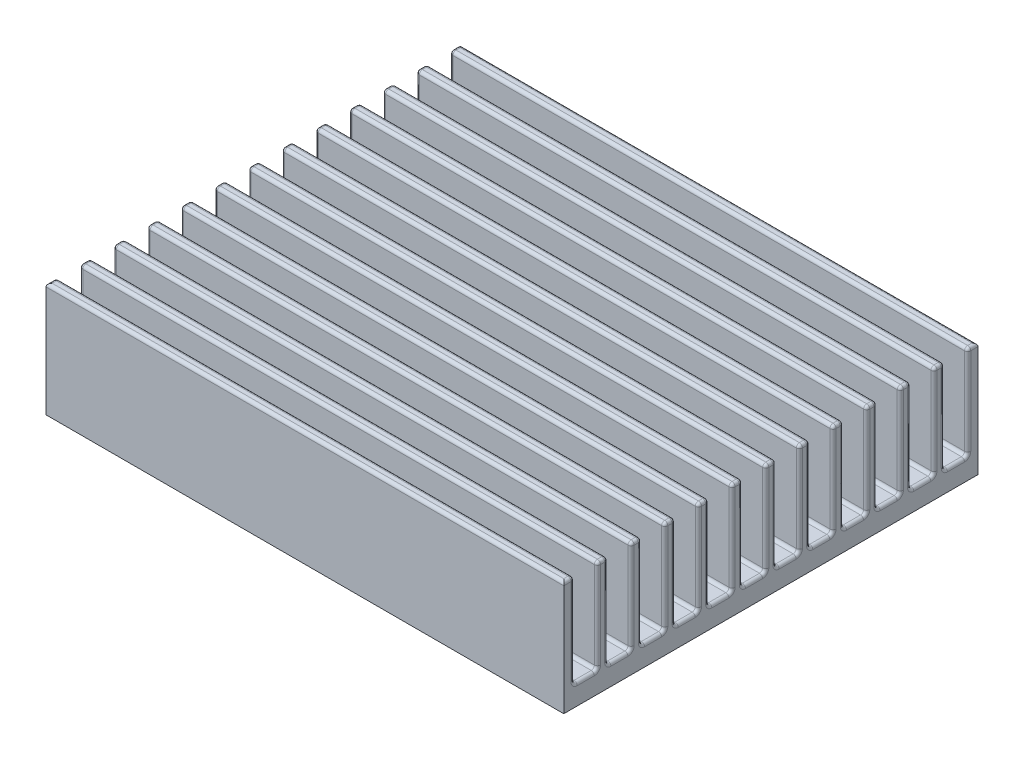
SolidWorks part; units mm, degrees
material "1060 Alloy"
ref_plane "Front" through (0, 0, 0) normal (0, 0, 1) x (1, 0, 0)
ref_plane "Top" through (0, 0, 0) normal (0, 1, 0) x (1, 0, 0)
ref_plane "Right" through (0, 0, 0) normal (1, 0, 0) x (0, 0, -1)
sketch "Sketch1" plane through (0, 0, 0) normal (0, 1, 0) x (1, 0, 0)
  line L1 (-25, -20) -> (25, -20)
  line L2 (-25, -20) -> (-25, 20)
  line L3 (-25, 20) -> (25, 20)
  line L4 (25, -20) -> (25, 20)
  line L5 (-25, -20) -> (25, 20) construction
  line L6 (-25, 20) -> (25, -20) construction
  point P0 (0, 0)
  dimension "D1" = 50
  dimension "D2" = 40
extrude "Boss-Extrude1" add sketch "Sketch1" along normal blind 2
sketch "Sketch2" plane through (25, 0, 0) normal (1, 0, 0) x (0, 0, -1)
  line L0 (-20, 11) -> (-20, 2)
  line L1 (-20, 11) -> (-19, 11)
  line L2 (-19, 11) -> (-19, 2)
  line L3 (-20, 2) -> (20, 2) construction
  line L4 (-16.75, 11) -> (-16.75, 2)
  line L5 (-16.75, 11) -> (-15.75, 11)
  line L6 (-15.75, 11) -> (-15.75, 2)
  line L7 (-16.75, 2) -> (-15.75, 2)
  line L8 (-13.5, 11) -> (-13.5, 2)
  line L9 (-13.5, 11) -> (-12.5, 11)
  line L10 (-12.5, 11) -> (-12.5, 2)
  line L11 (-13.5, 2) -> (-12.5, 2)
  line L12 (-10.25, 11) -> (-10.25, 2)
  line L13 (-10.25, 11) -> (-9.25, 11)
  line L14 (-9.25, 11) -> (-9.25, 2)
  line L15 (-10.25, 2) -> (-9.25, 2)
  line L16 (-7, 11) -> (-7, 2)
  line L17 (-7, 11) -> (-6, 11)
  line L18 (-6, 11) -> (-6, 2)
  line L19 (-7, 2) -> (-6, 2)
  line L20 (-3.75, 11) -> (-3.75, 2)
  line L21 (-3.75, 11) -> (-2.75, 11)
  line L22 (-2.75, 11) -> (-2.75, 2)
  line L23 (-3.75, 2) -> (-2.75, 2)
  line L24 (-0.5, 11) -> (-0.5, 2)
  line L25 (-0.5, 11) -> (0.5, 11)
  line L26 (0.5, 11) -> (0.5, 2)
  line L27 (-0.5, 2) -> (0.5, 2)
  line L28 (2.75, 11) -> (2.75, 2)
  line L29 (2.75, 11) -> (3.75, 11)
  line L30 (3.75, 11) -> (3.75, 2)
  line L31 (2.75, 2) -> (3.75, 2)
  line L32 (6, 11) -> (6, 2)
  line L33 (6, 11) -> (7, 11)
  line L34 (7, 11) -> (7, 2)
  line L35 (6, 2) -> (7, 2)
  line L36 (9.25, 11) -> (9.25, 2)
  line L37 (9.25, 11) -> (10.25, 11)
  line L38 (10.25, 11) -> (10.25, 2)
  line L39 (9.25, 2) -> (10.25, 2)
  line L40 (-20, 2) -> (-19, 2)
  line L41 (12.5, 11) -> (12.5, 2)
  line L42 (12.5, 11) -> (13.5, 11)
  line L43 (13.5, 11) -> (13.5, 2)
  line L44 (12.5, 2) -> (13.5, 2)
  line L45 (15.75, 11) -> (15.75, 2)
  line L46 (15.75, 11) -> (16.75, 11)
  line L47 (16.75, 11) -> (16.75, 2)
  line L48 (15.75, 2) -> (16.75, 2)
  line L49 (19, 11) -> (19, 2)
  line L50 (19, 11) -> (20, 11)
  line L51 (20, 11) -> (20, 2)
  line L52 (19, 2) -> (20, 2)
  line L53 (-20, 0) -> (20, 0) construction
  point P0 (20, 2)
  dimension "D1" = 1
  dimension "D2" = 11
extrude "Boss-Extrude2" add sketch "Sketch2" against normal up to surface (50 mm away) up to face at (-25, 1, 0)
fillet "Fillet1" radius 0.3 148 edges at (25, 2, -17.875) (-25, 2, -17.875) (25, 2, -14.625) (-25, 2, -14.625) (25, 2, -11.375) (-25, 2, -11.375) (25, 2, -8.125) (-25, 2, -8.125) (25, 2, -4.875) (-25, 2, -4.875) (25, 2, -1.625) (-25, 2, -1.625) (25, 2, 1.625) (-25, 2, 1.625) (25, 2, 4.875) (-25, 2, 4.875) (25, 2, 8.125) (-25, 2, 8.125) (25, 2, 11.375) (-25, 2, 11.375) (25, 2, 14.625) (-25, 2, 14.625) (25, 2, 17.875) (-25, 2, 17.875) (-25, 11, -19.5) (25, 11, -19.5) (-25, 6.5, -19) (25, 6.5, -19) (0, 11, -19) (0, 2, -19) (0, 11, -20) (-25, 11, -16.25) (25, 11, -16.25) (-25, 6.5, -15.75) (25, 6.5, -15.75) (-25, 6.5, -16.75) (25, 6.5, -16.75) (0, 11, -15.75) (0, 2, -15.75) (0, 2, -16.75) (0, 11, -16.75) (-25, 11, -13) (25, 11, -13) (-25, 6.5, -12.5) (25, 6.5, -12.5) (-25, 6.5, -13.5) (25, 6.5, -13.5) (0, 11, -12.5) (0, 2, -12.5) (0, 2, -13.5) (0, 11, -13.5) (-25, 11, -9.75) (25, 11, -9.75) (-25, 6.5, -9.25) (25, 6.5, -9.25) (-25, 6.5, -10.25) (25, 6.5, -10.25) (0, 11, -9.25) (0, 2, -9.25) (0, 2, -10.25) (0, 11, -10.25) (-25, 11, -6.5) (25, 11, -6.5) (-25, 6.5, -6) (25, 6.5, -6) (-25, 6.5, -7) (25, 6.5, -7) (0, 11, -6) (0, 2, -6) (0, 2, -7) (0, 11, -7) (-25, 11, -3.25) (25, 11, -3.25) (-25, 6.5, -2.75) (25, 6.5, -2.75) (-25, 6.5, -3.75) (25, 6.5, -3.75) (0, 11, -2.75) (0, 2, -2.75) (0, 2, -3.75) (0, 11, -3.75) (-25, 11, 0) (25, 11, 0) (-25, 6.5, 0.5) (25, 6.5, 0.5) (-25, 6.5, -0.5) (25, 6.5, -0.5) (0, 11, 0.5) (0, 2, 0.5) (0, 2, -0.5) (0, 11, -0.5) (-25, 11, 3.25) (25, 11, 3.25) (-25, 6.5, 3.75) (25, 6.5, 3.75) (-25, 6.5, 2.75) (25, 6.5, 2.75) (0, 11, 3.75) (0, 2, 3.75) (0, 2, 2.75) (0, 11, 2.75) (-25, 11, 6.5) (25, 11, 6.5) (-25, 6.5, 7) (25, 6.5, 7) (-25, 6.5, 6) (25, 6.5, 6) (0, 11, 7) (0, 2, 7) (0, 2, 6) (0, 11, 6) (-25, 11, 9.75) (25, 11, 9.75) (-25, 6.5, 10.25) (25, 6.5, 10.25) (-25, 6.5, 9.25) (25, 6.5, 9.25) (0, 11, 10.25) (0, 2, 10.25) (0, 2, 9.25) (0, 11, 9.25) (-25, 11, 13) (25, 11, 13) (-25, 6.5, 13.5) (25, 6.5, 13.5) (-25, 6.5, 12.5) (25, 6.5, 12.5) (0, 11, 13.5) (0, 2, 13.5) (0, 2, 12.5) (0, 11, 12.5) (-25, 11, 16.25) (25, 11, 16.25) (-25, 6.5, 16.75) (25, 6.5, 16.75) (-25, 6.5, 15.75) (25, 6.5, 15.75) (0, 11, 16.75) (0, 2, 16.75) (0, 2, 15.75) (0, 11, 15.75) (-25, 11, 19.5) (25, 11, 19.5) (-25, 6.5, 19) (25, 6.5, 19) (0, 11, 20) (0, 2, 19) (0, 11, 19)
sketch "Sketch3" plane through (0, 0, 0) normal (0, -1, 0) x (1, 0, 0)
  line L0 (-25, -7) -> (25, -7) construction
  line L2 (25, 20) -> (25, -20) construction
  line L3 (0, 0) -> (0, -7) construction
  line L4 (-25, -20) -> (-25, 20) construction
  circle A0 centre (-15, -7) radius 1.5
  circle A1 centre (15, -7) radius 1.5
  point P2 (-25, -7)
  point P3 (0, 0)
  point P14 (0, 0)
  point P15 (0, 0)
  point P16 (-25, -7)
  point P17 (-25, -7)
  point P20 (0, 0)
  dimension "D2" = 3
  dimension "D1" = 13
  dimension "D3" = 30
  dimension "D4" = 10
extrude "Cut-Extrude1" cut sketch "Sketch3" against normal blind 2
